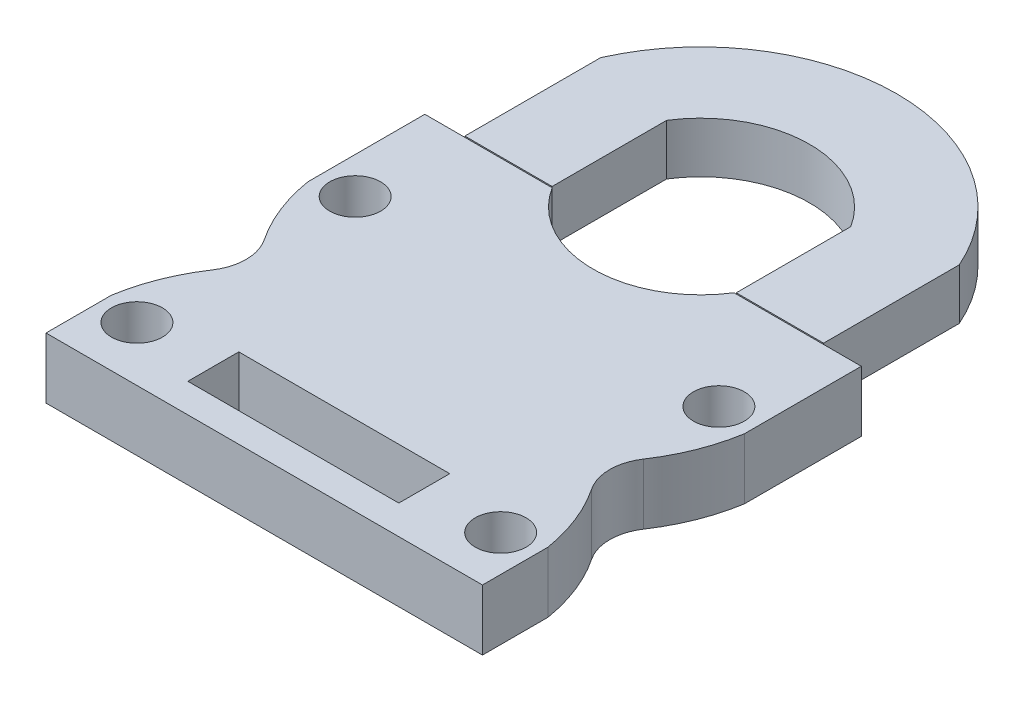
SolidWorks part; units mm, degrees
ref_plane "Front Plane" through (0, 0, 0) normal (0, 0, 1) x (1, 0, 0)
ref_plane "Top Plane" through (0, 0, 0) normal (0, 1, 0) x (1, 0, 0)
ref_plane "Right Plane" through (0, 0, 0) normal (1, 0, 0) x (0, 0, -1)
sketch "Sketch1" plane through (0, 0, 0) normal (0, 1, 0) x (1, 0, 0)
  line L0 (-38.1, -28.575) -> (38.1, -28.575)
  line L1 (31.75, -19.05) -> (-31.75, -19.05) construction
  line L2 (31.75, -19.05) -> (31.75, 19.05) construction
  line L3 (31.75, 19.05) -> (-31.75, 19.05) construction
  line L4 (-31.75, -19.05) -> (-31.75, 19.05) construction
  line L5 (31.75, -19.05) -> (-31.75, 19.05) construction
  line L6 (31.75, 19.05) -> (-31.75, -19.05) construction
  line L11 (38.1, -28.575) -> (38.1, 37.5615)
  line L13 (-38.1, 37.5615) -> (-38.1, -28.575)
  line L14 (-15.875, 37.5615) -> (-38.1, 37.5615)
  line L15 (0, -28.575) -> (0, 28.829) construction
  line L21 (15.875, 37.5615) -> (38.1, 37.5615)
  line L22 (0, 47.625) -> (0, -28.575) construction
  line L29 (0, 28.829) -> (0, -28.575) construction
  circle A0 centre (-31.75, 19.05) radius 2.8511
  circle A1 centre (31.75, 19.05) radius 2.8511
  circle A2 centre (31.75, -19.05) radius 2.8511
  circle A3 centre (-31.75, -19.05) radius 2.8511
  arc A4 (-15.875, 37.5615) -> (15.875, 37.5615) centre (0, 47.625) ccw
  point P0 (0, 0)
  point P10 (0, 0)
  dimension "D3" = 5.7023
  dimension "D8" = 37.592
  dimension "D1" = 63.5
  dimension "D2" = 38.1
  dimension "D4" = 76.2
  dimension "D5" = 9.525
  dimension "D6" = 22.225
  dimension "D7" = 76.2
  dimension "D9" = 66.1365
extrude "Boss-Extrude1" add sketch "Sketch1" along normal blind 10.6045
sketch "Sketch2" plane through (0, 10.6045, 0) normal (0, 1, 0) x (1, 0, 0)
  circle A0 centre (-31.75, 19.05) radius 4.445
  circle A1 centre (31.75, 19.05) radius 4.445
  circle A2 centre (31.75, -19.05) radius 4.445
  circle A3 centre (-31.75, -19.05) radius 4.445
  dimension "D1" = 8.89
  dimension "D2" = 8.89
  dimension "D3" = 8.89
  dimension "D4" = 8.89
extrude "Cut-Extrude1" cut sketch "Sketch2" against normal blind 7.9121
sketch "Sketch3" plane through (0, 0, -37.5615) normal (0, 0, -1) x (-1, 0, 0)
  line L0 (15.875, 0) -> (15.875, 5.3022) construction
  line L1 (15.875, 9.017) -> (25.4, 9.017)
  line L2 (15.875, 9.017) -> (15.875, 1.5875)
  line L3 (15.875, 1.5875) -> (25.4, 1.5875)
  line L4 (25.4, 9.017) -> (25.4, 1.5875)
  line L6 (15.875, 0) -> (38.1, 0) construction
  line L7 (15.875, 10.6045) -> (38.1, 10.6045) construction
  line L8 (38.1, 10.6045) -> (38.1, 0) construction
  line L9 (15.875, 10.6045) -> (15.875, 0) construction
  dimension "D2" = 1.5875
  dimension "D3" = 1.5875
  dimension "D4" = 12.7
extrude "Cut-Extrude2" cut sketch "Sketch3" against normal blind 38.1
mirror "Mirror1" about plane through (0, 0, 0) normal (1, 0, 0) of "Cut-Extrude2"
sketch "Sketch4" plane through (-38.1, 0, 0) normal (-1, 0, 0) x (0, 0, 1)
  line L0 (0.5385, 9.017) -> (-37.5615, 9.017) construction
  line L5 (-14.605, 6.6484) -> (14.605, 6.6484) construction
  line L6 (-14.605, 2.6924) -> (-14.605, 10.6045) construction
  line L7 (14.605, 10.6045) -> (14.605, 2.6924) construction
  line L9 (0, 0) -> (0, 10.6045) construction
  line L10 (-37.5615, 10.6045) -> (28.575, 10.6045) construction
  line L11 (6.985, 1.5875) -> (-6.985, 1.5875)
  line L12 (6.985, 1.5875) -> (6.985, 9.017)
  line L13 (6.985, 9.017) -> (-6.985, 9.017)
  line L14 (-6.985, 1.5875) -> (-6.985, 9.017)
  line L15 (6.985, 1.5875) -> (-6.985, 9.017) construction
  line L16 (6.985, 9.017) -> (-6.985, 1.5875) construction
  line L17 (-37.5615, 5.3022) -> (-6.985, 5.3022) construction
  line L18 (-37.5615, 10.6045) -> (-37.5615, 0) construction
  point P4 (0, 5.3022)
  dimension "D1" = 7.62
ref_plane "Plane1" through (0, 5.3022, 0) normal (0, 1, 0) x (1, 0, 0)
sketch "Sketch7" plane through (0, 5.3022, 0) normal (0, 1, 0) x (1, 0, 0)
  line L0 (-38.1, 17.145) -> (-38.1, 0)
  line L3 (-38.1, 37.5615) -> (-38.1, -28.575) construction
  line L4 (-31.75, 0) -> (-38.1, 0) construction
  line L6 (-38.1, 0) -> (-31.75, 0)
  arc A2 (-38.1, 17.145) -> (-33.1277, 4.5406) centre (-6.5317, 22.3156) ccw
  arc A3 (-33.1277, 4.5406) -> (-31.75, 0) centre (-39.9217, 0) cw
  dimension "D1" = 6.35
  dimension "D3" = 8.1717
  dimension "D2" = 31.9889
  dimension "D4" = 17.145
extrude "Cut-Extrude7" cut sketch "Sketch7" against normal mid plane 11.43
mirror "Mirror4" about plane through (0, 0, 0) normal (1, 0, 0) of "Cut-Extrude7"
sketch "Sketch8" plane through (0, 5.3022, 0) normal (0, 1, 0) x (1, 0, 0)
  line L0 (0, -28.575) -> (0, 47.625) construction
  line L1 (-38.1, -28.575) -> (38.1, -28.575) construction
  line L2 (-15.875, -0.5385) -> (-15.875, 37.5615) construction
  line L3 (15.875, -0.5385) -> (15.875, 37.5615) construction
  line L4 (16.0734, 37.7599) -> (16.0734, 57.7459)
  line L5 (-16.0734, 37.7599) -> (-16.0734, 57.7459)
  line L6 (31.3134, 37.7599) -> (31.3134, 61.4621)
  line L7 (-31.3134, 37.7599) -> (-31.3134, 61.4621)
  line L8 (31.3134, 37.7599) -> (31.3134, 61.4621) construction
  line L9 (31.3134, 37.7599) -> (25.2016, 37.7599)
  line L10 (-25.2016, 37.7599) -> (-25.2016, 0)
  line L11 (-25.2016, 0) -> (-16.0734, 0)
  line L12 (-16.0734, 0) -> (-16.0734, 37.7599)
  line L13 (25.2016, 37.7599) -> (25.2016, 0)
  line L14 (25.2016, 0) -> (16.0734, 0)
  line L15 (16.0734, 0) -> (16.0734, 37.7599)
  line L16 (38.1, 37.5615) -> (15.875, 37.5615) construction
  line L20 (-31.3134, 37.7599) -> (-25.2016, 37.7599)
  line L28 (-31.3134, 37.7599) -> (-31.3134, 61.4621) construction
  circle A0 centre (0, 47.625) radius 18.796 construction
  arc A1 (16.0734, 57.7459) -> (-16.0734, 57.7459) centre (0, 47.625) ccw
  circle A2 centre (0, 47.625) radius 18.9944 construction
  arc A3 (31.3134, 61.4621) -> (-31.3134, 61.4621) centre (0, 47.625) ccw
  dimension "D2" = 37.592
  dimension "D1" = 76.2
  dimension "D4" = 0.1984
  dimension "D5" = 0.1984
  dimension "D7" = 0.1984
  dimension "D8" = 50.4031
  dimension "D3" = 0.1984
  dimension "D6" = 15.24
extrude "Boss-Extrude3" add sketch "Sketch8" along normal mid plane 7.1295 separate body
sketch "Sketch13" plane through (0, 10.6045, 0) normal (0, 1, 0) x (1, 0, 0)
  line L0 (-38.1, -28.575) -> (38.1, -28.575) construction
  line L1 (18.415, -23.495) -> (-18.415, -23.495)
  line L2 (18.415, -23.495) -> (18.415, -14.605)
  line L3 (18.415, -14.605) -> (-18.415, -14.605)
  line L4 (-18.415, -23.495) -> (-18.415, -14.605)
  line L5 (18.415, -23.495) -> (-18.415, -14.605) construction
  line L6 (18.415, -14.605) -> (-18.415, -23.495) construction
  point P0 (0, -19.05)
  dimension "D1" = 36.83
  dimension "D2" = 8.89
  dimension "D3" = 5.08
extrude "Cut-Extrude10" cut sketch "Sketch13" against normal through all
mirror "Mirror6" about plane through (0, 0, 0) normal (0, 0, 1) of "Mirror4", "Cut-Extrude7"
sketch "Sketch18" plane through (0, 8.867, 0) normal (0, 1, 0) x (1, 0, 0)
  line L0 (-31.3134, 37.7599) -> (-16.0734, 37.7599)
  line L1 (-16.0734, 0) -> (-16.0734, 57.7459) construction
  line L2 (-16.0734, 37.7599) -> (-16.0734, 57.7459)
  line L3 (-31.3134, 37.7599) -> (-31.3134, 61.4621)
  line L4 (16.0734, 57.7459) -> (16.0734, 37.7599)
  line L5 (16.0734, 0) -> (16.0734, 57.7459) construction
  line L6 (16.0734, 37.7599) -> (31.3134, 37.7599)
  line L7 (31.3134, 37.7599) -> (31.3134, 61.4621) construction
  line L8 (31.3134, 37.7599) -> (31.3134, 61.4621)
  arc A0 (31.3134, 61.4621) -> (-31.3134, 61.4621) centre (0, 47.625) ccw construction
  arc A1 (31.3134, 61.4621) -> (-31.3134, 61.4621) centre (0, 47.625) ccw
  arc A2 (16.0734, 57.7459) -> (-16.0734, 57.7459) centre (0, 47.625) ccw construction
  arc A3 (16.0734, 57.7459) -> (-16.0734, 57.7459) centre (0, 47.625) ccw
extrude "Boss-Extrude5" add sketch "Sketch18" along normal up to surface (1.7375 mm away) up to face at (0, 10.6045, -6.026)
